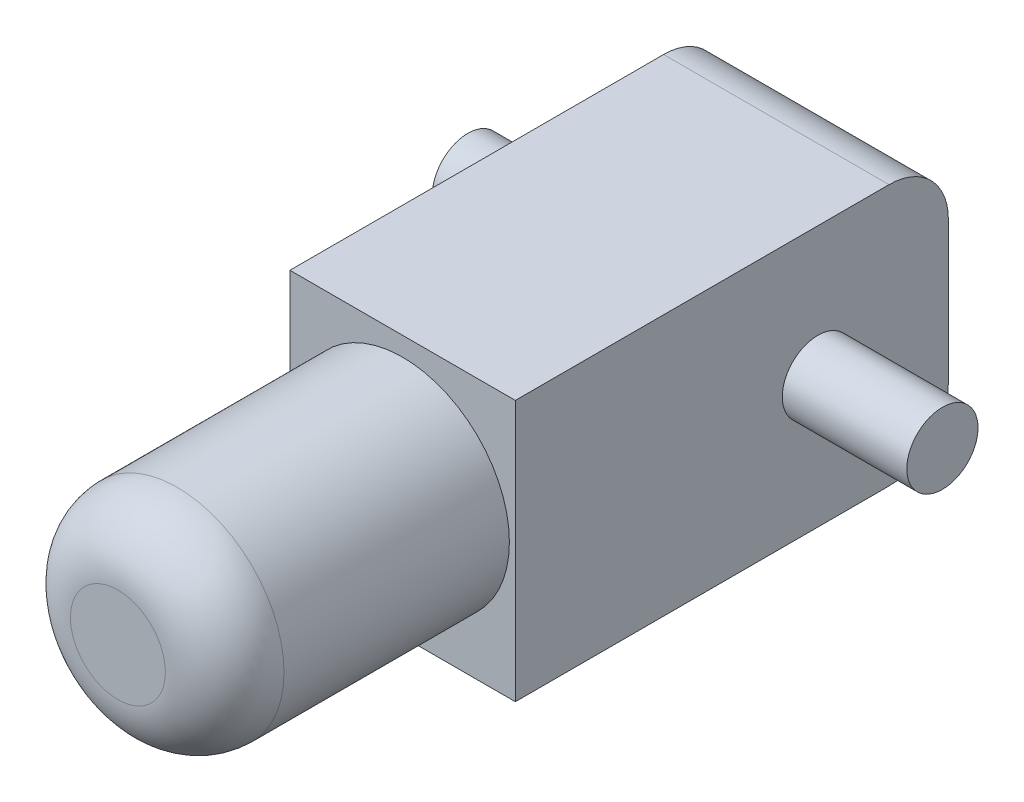
SolidWorks part; units mm, degrees
ref_plane "前视基准面" through (0, 0, 0) normal (0, 0, 1) x (1, 0, 0)
ref_plane "上视基准面" through (0, 0, 0) normal (0, 1, 0) x (1, 0, 0)
ref_plane "右视基准面" through (0, 0, 0) normal (1, 0, 0) x (0, 0, -1)
other "Configuration Table"
sketch "草图1" plane through (0, 0, 0) normal (1, 0, 0) x (0, 0, -1)
  line L1 (0, 0) -> (36.5, 0)
  line L2 (0, 0) -> (0, 22)
  line L3 (0, 22) -> (36.5, 22)
  line L4 (36.5, 0) -> (36.5, 22)
  point P5 (47.6017, 22)
  point P6 (48.0367, 22)
  point P7 (48.673, 27.4881)
  point P8 (84.878, 2.8326)
  dimension "D1" = 22
  dimension "D2" = 36.5
extrude "凸台-拉伸1" add sketch "草图1" along normal blind 19
ref_plane "基准面1" through (9.5, 0, 0) normal (1, 0, 0) x (0, 0, -1)
sketch "草图3" plane through (9.5, 0, 0) normal (1, 0, 0) x (0, 0, -1)
  line L0 (-2.2781, 11) -> (41.6917, 11) construction
  line L2 (36.5, 0) -> (36.5, 22) construction
  circle A0 centre (25.5, 11) radius 3
  point P3 (0, 0)
  dimension "D1" = 6
  dimension "D2" = 11
extrude "凸台-拉伸3" add sketch "草图3" along normal mid plane 40
fillet "圆角1" radius 5 2 edges at (9.5, 0, -36.5) (9.5, 22, -36.5)
sketch "草图4" plane through (0, 0, 0) normal (0, 0, 1) x (1, 0, 0)
  line L0 (9.5, 22) -> (9.5, -6.4079) construction
  line L3 (9.5, -12.1) -> (9.5, 12.1) construction
  circle A0 centre (9.5, 11.4055) radius 9
  point P3 (9.5, 11.4055)
  dimension "D1" = 18
extrude "凸台-拉伸4" add sketch "草图4" along normal blind 24
fillet "圆角2" radius 5 1 edges at (18.5, 11.4055, 24)
